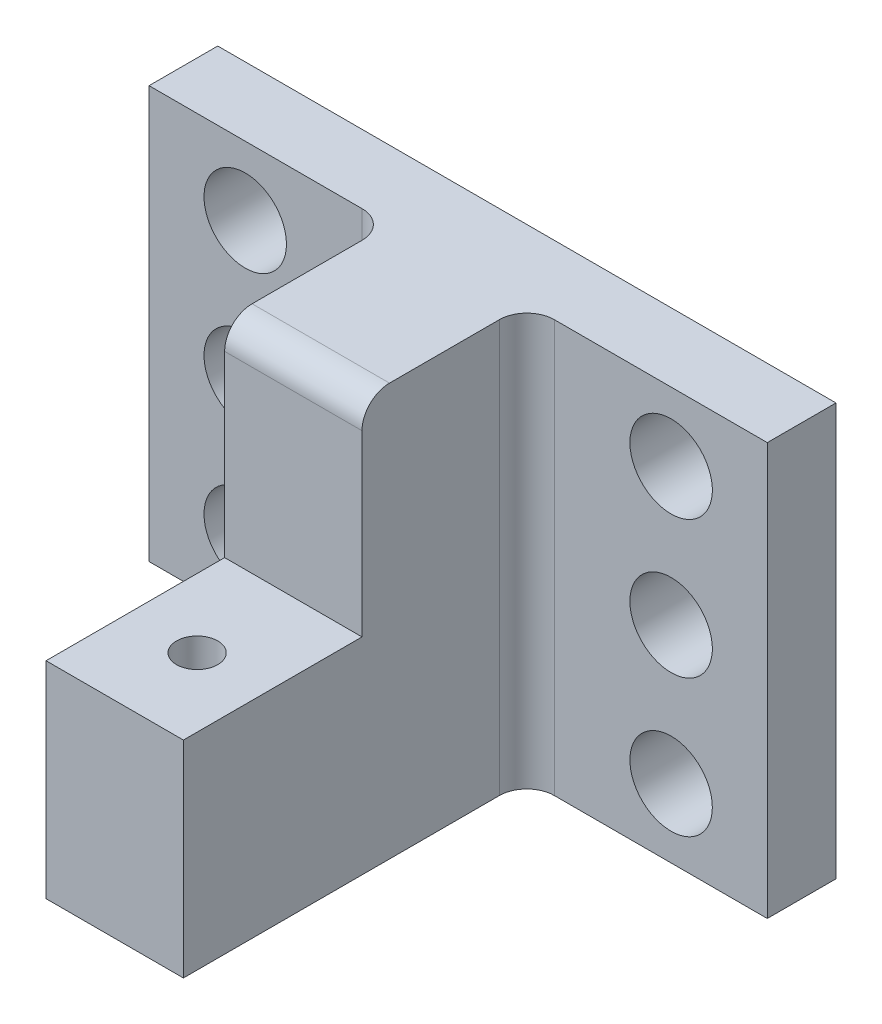
SolidWorks part; units mm, degrees
ref_plane "Piano frontale" through (0, 0, 0) normal (0, 0, 1) x (1, 0, 0)
ref_plane "Piano superiore" through (0, 0, 0) normal (0, 1, 0) x (1, 0, 0)
ref_plane "Piano destro" through (0, 0, 0) normal (1, 0, 0) x (0, 0, -1)
sketch "Sketch1" plane through (0, 0, 0) normal (0, 0, 1) x (1, 0, 0)
  line L0 (-22.5, 15) -> (22.5, -15) construction
  line L1 (-22.5, 15) -> (22.5, 15)
  line L2 (-22.5, 15) -> (-22.5, -15)
  line L3 (-22.5, -15) -> (22.5, -15)
  line L4 (22.5, 15) -> (22.5, -15)
  line L5 (-22.5, -15) -> (22.5, 15) construction
  point P4 (0, 0)
  dimension "D1" = 30
  dimension "D2" = 45
extrude "Base" add sketch "Sketch1" along normal blind 5
sketch "Sketch2" plane through (0, 0, 5) normal (0, 0, 1) x (1, 0, 0)
  line L0 (-5, 15) -> (5, -15) construction
  line L1 (-5, 15) -> (5, 15)
  line L2 (-5, 15) -> (-5, -15)
  line L3 (-5, -15) -> (5, -15)
  line L4 (5, 15) -> (5, -15)
  line L5 (-5, -15) -> (5, 15) construction
  line L6 (22.5, 0) -> (-22.5, 0) construction
  line L7 (22.5, -15) -> (22.5, 15) construction
  line L8 (-22.5, 15) -> (-22.5, -15) construction
  point P10 (0, 0)
  dimension "D1" = 30
  dimension "D2" = 10
extrude "Boss-Extrude2" add sketch "Sketch2" along normal blind 25
sketch "Sketch5" plane through (0, -15, 0) normal (0, -1, 0) x (1, 0, 0)
  line L0 (-5, 30) -> (5, 30) construction
  line L1 (0, 30) -> (0, 24) construction
  circle A0 centre (0, 24) radius 1.5
  dimension "D1" = 3
  dimension "D2" = 6
extrude "Cable hole" cut sketch "Sketch5" against normal blind 15
sketch "Sketch9" plane through (0, 0, 5) normal (0, 0, 1) x (1, 0, 0)
  line L0 (-22.5, 10) -> (22.5, 10) construction
  line L2 (-22.5, 0) -> (22.5, 0) construction
  line L3 (-22.5, 15) -> (-22.5, -15) construction
  line L4 (22.5, -15) -> (22.5, 15) construction
  line L5 (0, 15) -> (0, -15) construction
  line L6 (22.5, 15) -> (5, 15) construction
  line L8 (-15.5, 10) -> (-15.5, -10) construction
  circle A1 centre (-15.5, 10) radius 3
  circle A2 centre (-15.5, 0) radius 3
  circle A7 centre (-15.5, -10) radius 3
  circle A8 centre (15.5, -10) radius 3
  circle A9 centre (15.5, 0) radius 3
  circle A10 centre (15.5, 10) radius 3
  dimension "D1" = 5
  dimension "D2" = 6
  dimension "D3" = 7
extrude "Screw" cut sketch "Sketch9" against normal blind 5
sketch "Sketch10" plane through (-5, 0, 0) normal (-1, 0, 0) x (0, 0, 1)
  line L0 (17, 10) -> (32, 10) construction
  line L1 (17, 20) -> (32, 20)
  line L2 (17, 20) -> (17, 0)
  line L3 (17, 0) -> (32, 0)
  line L4 (32, 20) -> (32, 0)
  line L5 (30, 15) -> (5, 15) construction
  line L6 (30, 15) -> (30, -15) construction
  dimension "D1" = 15
  dimension "D2" = 20
  dimension "D3" = 15
  dimension "D4" = 13
extrude "Cut-Extrude8" cut sketch "Sketch10" against normal blind 10
fillet "Fillet5" radius 2 1 edges at (0, 15, 17)
fillet "Fillet6" radius 2 1 edges at (-5, 0, 5)
fillet "Fillet7" radius 2 1 edges at (5, 0, 5)
